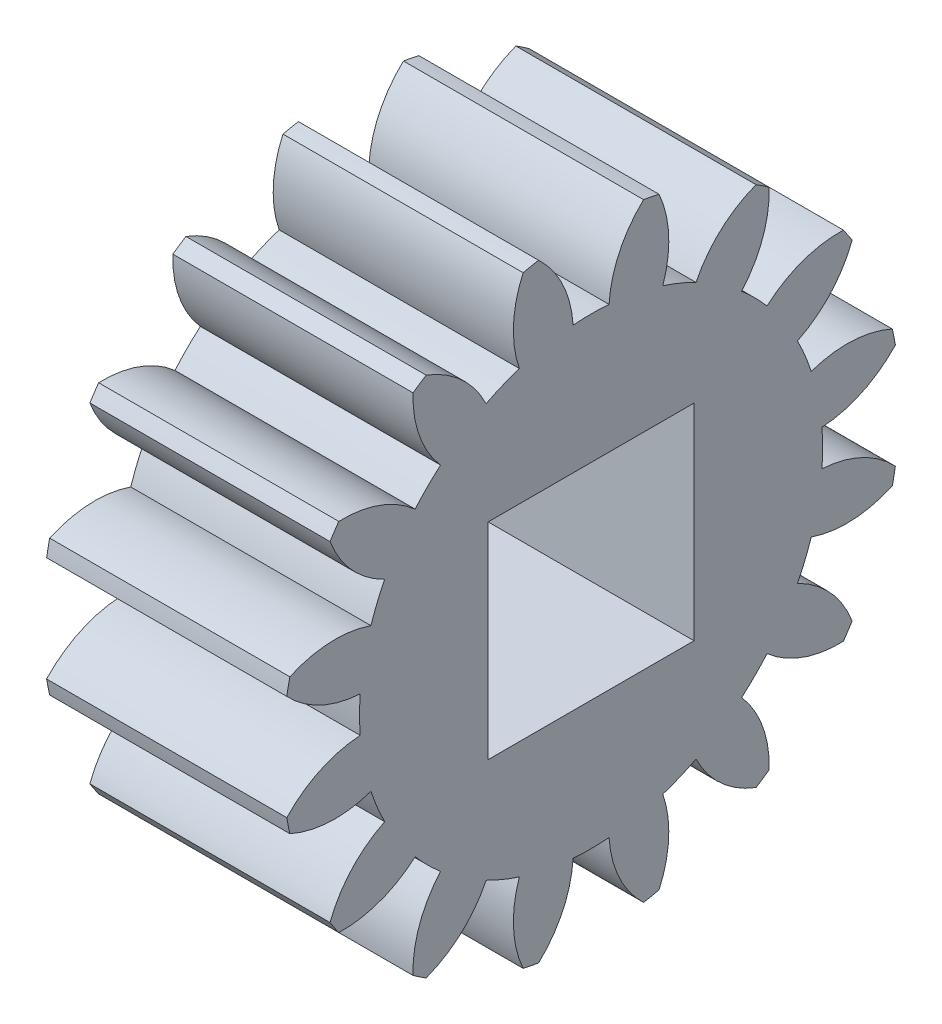
SolidWorks part; units mm, degrees
ref_plane "Plane1" through (0, 0, 0) normal (0, 0, 1) x (1, 0, 0)
ref_plane "Plane2" through (0, 0, 0) normal (0, 1, 0) x (1, 0, 0)
ref_plane "Plane3" through (0, 0, 0) normal (1, 0, 0) x (0, 0, -1)
sketch "HoldingSke" plane through (0, 0, 0) normal (0, 1, 0) x (1, 0, 0)
  line L0 (0, 0) -> (0.9613, -0.2756)
  line L1 (-15, 0) -> (100, 0) construction
  line L2 (0, 0) -> (-2.1039, 2.3779)
  line L3 (0, 0) -> (-11.863, 4.5341)
  line L4 (0, 0) -> (8.3015, 2.3804)
  line L5 (0, 0) -> (-46.8476, -17.4728)
  line L6 (0, 0) -> (-5.8027, -3.9151)
  line L7 (-2.1039, 2.3779) -> (8.6586, 51.2059)
  line L8 (-76.2, 54.61) -> (-75.2, 54.61)
  line L9 (-71.009, 38.7566) -> (-53.1078, 45.2721)
  line L10 (-76.2, 71.12) -> (104.1128, 71.12)
  line L11 (0, 0) -> (-5, 0)
  line L12 (-76.2, 101.6) -> (-76.162, 101.6)
  line L13 (24.9733, 27.94) -> (52.9518, 28.4284)
  line L14 (24.9733, 27.94) -> (24.9743, 27.94)
  line L15 (24.9733, 27.94) -> (100.4006, 29.5858)
  line L16 (-63.627, -1) -> (-12.827, -1)
  circle A0 centre (0, 0) radius 3
  circle A1 centre (0, 0) radius 6.749
  circle A2 centre (0, 0) radius 37.5
  circle A3 centre (0, 0) radius 3
  dimension "MHD" = 13.498
  dimension "Hub_dia" = 75
  dimension "Bore" = 6
  dimension "MBD" = 6
  dimension "Num_teeth" = 16
  dimension "Pitch_radius" = 180.3128
  dimension "Pitch" = 1
  dimension "Width" = 5
  dimension "Overall_len" = 50
  dimension "Show_teeth" = 16
  dimension "Thickness" = 7
  dimension "OAL" = 50.0001
  dimension "T_dim" = 1
  dimension "Ap" = 20
  dimension "H" = 19.05
  dimension "Backlash" = 0.038
  dimension "Addendum_fac" = 1
  dimension "Dedendum_fac" = 1.25
  dimension "Clearance_fac" = 0.25
  dimension "Dedendum_add" = 0.001
  dimension "Module" = 1
sketch "BasProSke" plane through (0, 0, 0) normal (0, 1, 0) x (1, 0, 0)
  line L0 (-10, 0) -> (60, 0) construction
  line L1 (0, 0) -> (0, 9)
  line L2 (0, 0) -> (7, 0)
  line L3 (7, 0) -> (7, 9)
  line L4 (7, 9) -> (0, 9)
  dimension "Diameter" = 18
  dimension "Thickness" = 7
revolve "Base-Revolve" add sketch "BasProSke" angle 360 about L0
sketch "TooCutSke" plane through (0, 0, 0) normal (1, 0, 0) x (0, 0, -1)
  line L1 (0, 0) -> (0, 107) construction
  line L2 (0, 0) -> (-0.8506, 7.9547) construction
  line L3 (0, 0) -> (-3.1089, 15.6293) construction
  line L4 (-0.8506, 7.9547) -> (-1.5544, 7.8146) construction
  arc A0 (0.5238, 6.7286) -> (-0.5238, 6.7286) centre (0, 0) ccw
  arc A1 (1.5534, 8.8907) -> (-1.5534, 8.8907) centre (0, 0) ccw
  circle A2 centre (0, 0) radius 8 construction
  circle A3 centre (0, 0) radius 7.5175 construction
  arc A4 (-0.5238, 6.7286) -> (-1.5534, 8.8907) centre (-3.7179, 6.5338) ccw
  arc A5 (1.5534, 8.8907) -> (0.5238, 6.7286) centre (3.7179, 6.5338) ccw
  dimension "Root_dia" = 13.498
  dimension "Overcut_dia" = 18.0508
  dimension "Pitch_dia" = 16
  dimension "Base_dia" = 15.0351
  dimension "Flank_rad" = 3.2
  dimension "Half_ang" = 11.25
  dimension "Half_CT" = 0.7176
extrude "ToothCut" cut sketch "TooCutSke" along normal through all
fillet "Breaks" [suppressed] radius 0.02
fillet "RootFillets" [suppressed] radius 0.251
pattern_circular "TeethCuts" count 16 over 360 about axis through (0, 0, 0) along (1, 0, 0) of "ToothCut", "RootFillets", "Breaks"
sketch "HubNeaOneSke" plane through (0, 0, 0) normal (-1, 0, 0) x (0, 0, 1)
  circle A0 centre (0, 0) radius 6.749
  dimension "Diameter" = 13.498
extrude "HubNearOne" [suppressed] add sketch "HubNeaOneSke" along normal blind 43.0001
sketch "HubNeaBotSke" plane through (0, 0, 0) normal (-1, 0, 0) x (0, 0, 1)
  circle A0 centre (0, 0) radius 6.749
  dimension "Diameter" = 13.498
extrude "HubNearBoth" [suppressed] add sketch "HubNeaBotSke" along normal blind 21.5001
ref_plane "FarPln" through (7, 0, 0) normal (1, 0, 0) x (0, 0, -1)
sketch "HubFarSke" plane through (7, 0, 0) normal (1, 0, 0) x (0, 0, -1)
  circle A0 centre (0, 0) radius 6.749
  dimension "Diameter" = 13.498
extrude "HubFar" [suppressed] add sketch "HubFarSke" along normal blind 21.5001
sketch "BorSke" plane through (0, 0, 0) normal (1, 0, 0) x (0, 0, -1)
  circle A0 centre (0, 0) radius 3
  dimension "Diameter" = 6
extrude "Bore" cut sketch "BorSke" along normal mid plane 100.0002
sketch "KeySke" plane through (0, 0, 0) normal (1, 0, 0) x (0, 0, -1)
  line L0 (-1, 0) -> (-1, 4)
  line L1 (-1, 4) -> (1, 4)
  line L2 (1, 4) -> (1, 0)
  line L3 (0, 0) -> (0, 34) construction
  line L4 (-1, 0) -> (1, 0)
  dimension "Offset" = 4
  dimension "Width" = 2
extrude "Keyway" [suppressed] cut sketch "KeySke" along normal mid plane 100.0002
pattern_circular "Keyway2" [suppressed] count 2 every 90 about axis through (-10, 0, 0) along (1, 0, 0)
sketch "Sketch1" plane through (7, 0, 0) normal (1, 0, 0) x (0, 0, -1)
  line L1 (-3, -3) -> (3, -3)
  line L2 (-3, -3) -> (-3, 3)
  line L3 (-3, 3) -> (3, 3)
  line L4 (3, -3) -> (3, 3)
  line L5 (-3, -3) -> (3, 3) construction
  line L6 (-3, 3) -> (3, -3) construction
  circle A0 centre (0, 0) radius 3 construction
  point P0 (0, 0)
  dimension "D1" = 0
  dimension "D2" = 6
  dimension "D3" = 6
extrude "Cut-Extrude1" cut sketch "Sketch1" against normal blind 10
equation "' \"Module@HoldingSke\" = 6.35"
equation "' \"Num_teeth@HoldingSke\" = 12"
equation "' \"Ap@HoldingSke\" =  20"
equation "' \"Width@HoldingSke\" = 0.5 * 25.4"
equation "' \"Hub_dia@HoldingSke\"= 1 * 25.4"
equation "' \"Overall_len@HoldingSke\" = 1.0 * 25.4"
equation "' \"Bore@HoldingSke\" = 0.75 * 25.4"
equation "' \"T_dim@HoldingSke\" = 0.1 * 25.4"
equation "' \"Width@KeySke\" = 0.25 * 25.4"
equation "' \"Show_teeth@HoldingSke\" = 13"
equation "' \"Backlash@HoldingSke\" = 0.009 * 25.4"
equation "' \"Addendum_fac@HoldingSke\" = 1.0"
equation "' \"Dedendum_fac@HoldingSke\" = 1.25"
equation "' \"Dedendum_add@HoldingSke\" = 0.00005 * 25.4"
equation "' \"Clearance_fac@HoldingSke\" = 0.25"
equation "\"Pitch@HoldingSke\" = 1 / \"Module@HoldingSke\""
equation "\"Overcut_dia@TooCutSke\" = (\"Num_teeth@HoldingSke\" + 2 * \"Addendum_fac@HoldingSke\") / \"Pitch@HoldingSke\" + 0.002 * 25.4"
equation "\"Pitch_dia@TooCutSke\" = \"Num_teeth@HoldingSke\" / \"Pitch@HoldingSke\""
equation "\"Base_dia@TooCutSke\" = \"Num_teeth@HoldingSke\" / \"Pitch@HoldingSke\" * cos((\"Ap@HoldingSke\"  * 3.14159265 / 180))"
equation "\"Root_dia@TooCutSke\" = (\"Num_teeth@HoldingSke\" + 2) / \"Pitch@HoldingSke\" - 2 * (\"Addendum_fac@HoldingSke\" + \"Dedendum_fac@HoldingSke\") / \"Pitch@HoldingSke\" - \"Dedendum_add@HoldingSke\" * 2"
equation "\"Half_ang@TooCutSke\" = 180 / \"Num_teeth@HoldingSke\""
equation "\"Half_CT@TooCutSke\" = \"Num_teeth@HoldingSke\" / \"Pitch@HoldingSke\" * sin((3.14159265 / 2 / \"Num_teeth@HoldingSke\")) / 2 - 7 * \"Backlash@HoldingSke\" / 4"
equation "\"Flank_rad@TooCutSke\" = \"Num_teeth@HoldingSke\" / \"Pitch@HoldingSke\" / 5"
equation "\"Radius@RootFillets\" = \"Clearance_fac@HoldingSke\" / \"Pitch@HoldingSke\" + \"Dedendum_add@HoldingSke\""
equation "\"Break_rad@Breaks\" = 0.02 / \"Pitch@HoldingSke\""
equation "\"Thickness@HoldingSke\"= 7mm"
equation "\"OAL@HoldingSke\" = \"Thickness@HoldingSke\""
equation "\"MHD@HoldingSke\" = (\"Num_teeth@HoldingSke\" + 2) / \"Pitch@HoldingSke\" - 2 * (\"Addendum_fac@HoldingSke\" + \"Dedendum_fac@HoldingSke\")  / \"Pitch@HoldingSke\" - \"Dedendum_add@HoldingSke\" * 2"
equation "\"MBD@HoldingSke\" = (\"Num_teeth@HoldingSke\" + 2) / \"Pitch@HoldingSke\" - 2 * (\"Addendum_fac@HoldingSke\" + \"Dedendum_fac@HoldingSke\")  / \"Pitch@HoldingSke\" - \"Dedendum_add@HoldingSke\" * 2 - 0.002 * 25.4"
equation "\"MHD@HoldingSke\" = ((sgn( \"MHD@HoldingSke\" - \"Hub_dia@HoldingSke\" )-1)*( \"MHD@HoldingSke\" - \"Hub_dia@HoldingSke\" ))/-2+ \"Hub_dia@HoldingSke\""
equation "\"MBD@HoldingSke\" = ((sgn( \"MBD@HoldingSke\" - \"Bore@HoldingSke\" )-1)*( \"MBD@HoldingSke\" - \"Bore@HoldingSke\" ))/-2+ \"Bore@HoldingSke\""
equation "\"OAL@HoldingSke\" = ((sgn( \"OAL@HoldingSke\" - \"Overall_len@HoldingSke\" )+1)*( \"OAL@HoldingSke\" - \"Overall_len@HoldingSke\" ))/2 + \"Overall_len@HoldingSke\" + 0.000002 * 25.4"
equation "\"Num_teeth@TeethCuts\" = int( \"Show_teeth@HoldingSke\" ) + 1"
equation "\"Num_teeth@TeethCuts\" = ((sgn( \"Num_teeth@TeethCuts\" - \"Num_teeth@HoldingSke\" )-1)*( \"Num_teeth@TeethCuts\" - \"Num_teeth@HoldingSke\" ))/-2+ \"Num_teeth@HoldingSke\""
equation "\"Num_teeth@TeethCuts\" = ((sgn( \"Num_teeth@TeethCuts\" - 2.0)+1)*( \"Num_teeth@TeethCuts\" - 2.0))/2 +2.0"
equation "\"Angle@TeethCuts\" = 360.0 / \"Num_teeth@HoldingSke\""
equation "\"Diameter@BasProSke\" = (\"Num_teeth@HoldingSke\" + 2 * \"Addendum_fac@HoldingSke\") / \"Pitch@HoldingSke\""
equation "\"Thickness@BasProSke\"  = \"Thickness@HoldingSke\""
equation "' \"Fillet_rad@BasProSke\" =  \"Thickness@HoldingSke\" * 0.05"
equation "\"MHD@HoldingSke\" = ((sgn( \"MHD@HoldingSke\" - \"Root_dia@TooCutSke\" )-1)*( \"MHD@HoldingSke\" - \"Root_dia@TooCutSke\" ))/-2+ \"Root_dia@TooCutSke\""
equation "\"Diameter@HubNeaOneSke\" = \"MHD@HoldingSke\""
equation "\"Length@HubNearOne\" = \"OAL@HoldingSke\" - \"Thickness@BasProSke\""
equation "\"Diameter@HubNeaBotSke\" = \"MHD@HoldingSke\""
equation "\"Length@HubNearBoth\" = ( \"OAL@HoldingSke\" - \"Thickness@BasProSke\" ) / 2.0"
equation "\"Thickness@FarPln\" = \"Thickness@BasProSke\""
equation "\"Diameter@HubFarSke\" = \"MHD@HoldingSke\""
equation "\"Length@HubFar\" = ( \"OAL@HoldingSke\" - \"Thickness@BasProSke\" ) / 2.0"
equation "\"Diameter@BorSke\" = \"MBD@HoldingSke\""
equation "\"D1@Bore\" = \"OAL@HoldingSke\" * 2.0"
equation "\"D1@Keyway\" = \"OAL@HoldingSke\" * 2.0"
equation "\"Offset@KeySke\" = \"T_dim@HoldingSke\" + \"MBD@HoldingSke\" / 2.0"
